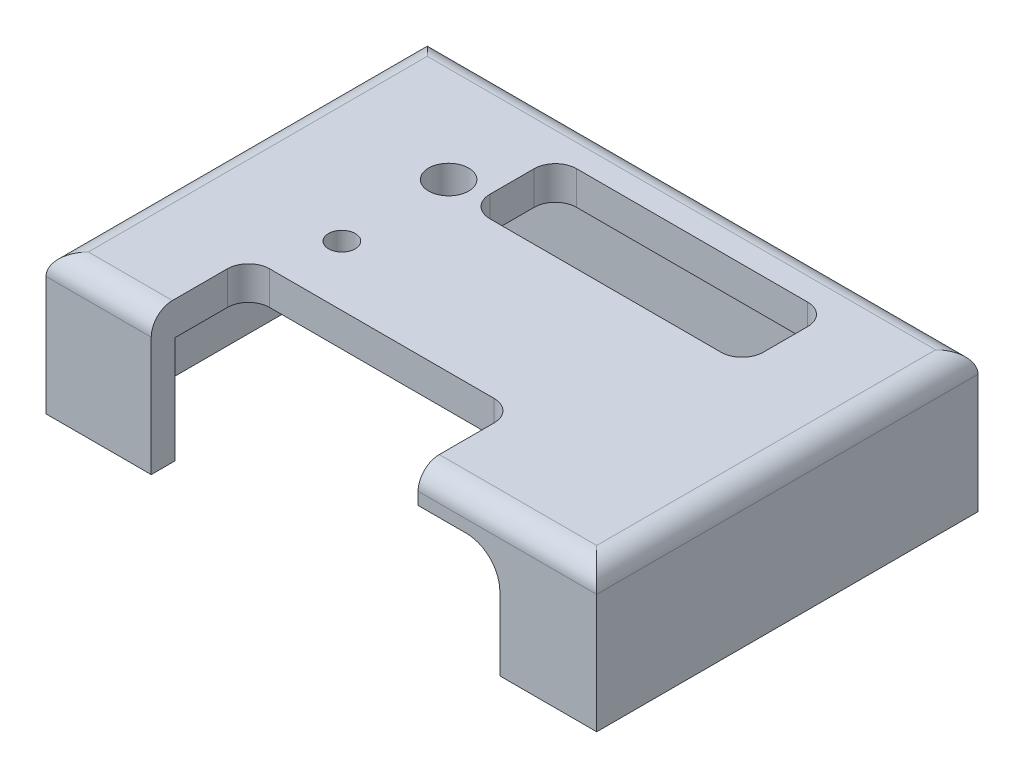
SolidWorks part; units mm, degrees
material "6061-T6 (SS)"
ref_plane "Front Plane" through (0, 0, 0) normal (0, 0, 1) x (1, 0, 0)
ref_plane "Top Plane" through (0, 0, 0) normal (0, 1, 0) x (1, 0, 0)
ref_plane "Right Plane" through (0, 0, 0) normal (1, 0, 0) x (0, 0, -1)
sketch "Sketch1" plane through (0, 0, 0) normal (0, 1, 0) x (1, 0, 0)
  line L1 (41.275, -28.575) -> (-41.275, -28.575)
  line L2 (41.275, -28.575) -> (41.275, 28.575)
  line L3 (41.275, 28.575) -> (-41.275, 28.575)
  line L4 (-41.275, -28.575) -> (-41.275, 28.575)
  line L5 (41.275, -28.575) -> (-41.275, 28.575) construction
  line L6 (41.275, 28.575) -> (-41.275, -28.575) construction
  point P0 (0, 0)
  dimension "D1" = 57.15
  dimension "D2" = 82.55
extrude "Boss-Extrude1" add sketch "Sketch1" along normal blind 21.018
sketch "Sketch2" plane through (0, 0, 0) normal (0, 1, 0) x (1, 0, 0)
  line L1 (30.15, -25) -> (-30.15, -25)
  line L2 (36.5, -18.65) -> (36.5, 18.65)
  line L3 (30.15, 25) -> (-30.15, 25)
  line L4 (-36.5, -18.65) -> (-36.5, 18.65)
  line L5 (36.5, -25) -> (-36.5, 25) construction
  line L6 (36.5, 25) -> (-36.5, -25) construction
  arc A0 (36.5, 18.65) -> (30.15, 25) centre (30.15, 18.65) ccw
  arc A1 (30.15, -25) -> (36.5, -18.65) centre (30.15, -18.65) ccw
  arc A2 (-30.15, -25) -> (-36.5, -18.65) centre (-30.15, -18.65) cw
  arc A3 (-30.15, 25) -> (-36.5, 18.65) centre (-30.15, 18.65) ccw
  point P0 (0, 0)
  dimension "D3" = 6.35
  dimension "D1" = 73
  dimension "D2" = 50
extrude "Cut-Extrude1" cut sketch "Sketch2" along normal blind 16
hole_wizard "#8-32 Tapped Hole1" positions "Sketch3" profile "Sketch4" tap size "#8-32" standard "ANSI Inch"
sketch "Sketch3" plane through (0, 0, 0) normal (0, -1, 0) x (-1, 0, 0)
  point P0 (37.275, -24.575)
  point P3 (37.275, 24.575)
  point P6 (-37.275, -24.575)
  point P9 (-37.275, 24.575)
cosmetic thread "Hole Thread1" parameters "D1"=8.331, "D2"=4.1656
cosmetic thread "Hole Thread2" parameters "D1"=8.331, "D2"=4.1656
cosmetic thread "Hole Thread3" parameters "D1"=8.331, "D2"=4.1656
cosmetic thread "Hole Thread4" parameters "D1"=8.331, "D2"=4.1656
sketch "Sketch4" plane through (-37.275, 0, 24.575) normal (1, 0, 0) x (0, 0, -1)
  line L0 (0, 0) -> (0, 11.7458)
  line L1 (0, 11.7458) -> (1.7272, 10.708)
  line L2 (1.7272, 10.708) -> (1.7272, 0)
  line L5 (1.7272, 0) -> (0, 0)
  line L10 (0, 11.7458) -> (-1.7272, 10.708) construction
  line L11 (0, -6.35) -> (0, 107.95) construction
  dimension "Tap Drill Dia." = 3.4544
  dimension "Tap Drill Depth" = 10.708
  dimension "Drill Angle" = 118
sketch "Sketch5" plane through (0, 21.018, 0) normal (0, 1, 0) x (1, 0, 0)
  line L5 (-15.5, 22) -> (-15.5, 9) construction
  line L6 (-15.5, 9) -> (25.5, 9) construction
  line L7 (25.5, 9) -> (25.5, 22) construction
  line L8 (25.5, 22) -> (-15.5, 22) construction
  line L9 (15, -6) -> (15, -22) construction
  line L10 (15, -22) -> (24.5, -22) construction
  line L11 (24.5, -22) -> (24.5, -6) construction
  line L12 (24.5, -6) -> (15, -6) construction
  line L13 (11, -20.5) -> (11, -15.5) construction
  line L14 (11, -15.5) -> (6, -15.5) construction
  line L15 (6, -15.5) -> (6, -20.5) construction
  line L16 (6, -20.5) -> (11, -20.5) construction
  line L17 (-3, -20.5) -> (-3, -15.5) construction
  line L18 (-3, -15.5) -> (-8, -15.5) construction
  line L19 (-8, -15.5) -> (-8, -20.5) construction
  line L20 (-8, -20.5) -> (-3, -20.5) construction
  line L21 (-17, -20.5) -> (-17, -15.5) construction
  line L22 (-17, -15.5) -> (-22, -15.5) construction
  line L23 (-22, -15.5) -> (-22, -20.5) construction
  line L24 (-22, -20.5) -> (-17, -20.5) construction
  line L25 (-15.5, 22) -> (-15.5, 9)
  line L26 (-15.5, 9) -> (25.5, 9)
  line L27 (25.5, 9) -> (25.5, 22)
  line L28 (25.5, 22) -> (-15.5, 22)
  line L29 (15, -6) -> (15, -22)
  line L30 (15, -22) -> (24.5, -22)
  line L31 (24.5, -22) -> (24.5, -6)
  line L32 (24.5, -6) -> (15, -6)
  line L33 (11, -20.5) -> (11, -15.5)
  line L34 (11, -15.5) -> (6, -15.5)
  line L35 (6, -15.5) -> (6, -20.5)
  line L36 (6, -20.5) -> (11, -20.5)
  line L37 (-3, -20.5) -> (-3, -15.5)
  line L38 (-3, -15.5) -> (-8, -15.5)
  line L39 (-8, -15.5) -> (-8, -20.5)
  line L40 (-8, -20.5) -> (-3, -20.5)
  line L41 (-17, -20.5) -> (-17, -15.5)
  line L42 (-17, -15.5) -> (-22, -15.5)
  line L43 (-22, -15.5) -> (-22, -20.5)
  line L44 (-22, -20.5) -> (-17, -20.5)
  circle A0 centre (-20.5, -5) radius 4.5 construction
  circle A1 centre (-20.5, 11) radius 4.5 construction
  circle A2 centre (-20.5, -5) radius 4.5
  circle A3 centre (-20.5, 11) radius 4.5
fillet "Fillet1" radius 3.175 4 edges at (0, 21.018, -28.575) (41.275, 21.018, 0) (0, 21.018, 28.575) (-41.275, 21.018, 0)
sketch "Sketch6" plane through (0, 21.018, 0) normal (0, 1, 0) x (1, 0, 0)
  line L0 (25.5, 15.5) -> (-15.5, 15.5) construction
  line L1 (-12.325, 9) -> (22.325, 9)
  line L2 (-15.5, 12.175) -> (-15.5, 18.825)
  line L3 (-12.325, 22) -> (22.325, 22)
  line L4 (25.5, 12.175) -> (25.5, 18.825)
  line L5 (-15.5, 9) -> (25.5, 22) construction
  line L6 (-15.5, 22) -> (25.5, 9) construction
  line L7 (25.5, 9) -> (25.5, 22) construction
  line L8 (-15.5, 22) -> (-15.5, 9) construction
  line L9 (-41.275, -28.575) -> (41.275, -28.575) construction
  line L10 (-25.5, -28.575) -> (14.5, -28.575)
  line L11 (-25.5, -28.575) -> (-25.5, -17.175)
  line L12 (-22.325, -14) -> (11.325, -14)
  line L13 (14.5, -28.575) -> (14.5, -17.175)
  line L14 (-5.5, -15.5) -> (-5.5, -14) construction
  line L15 (-3, -15.5) -> (-8, -15.5) construction
  line L16 (-22, -18) -> (11, -18) construction
  line L17 (-22, -15.5) -> (-22, -20.5) construction
  line L18 (11, -20.5) -> (11, -15.5) construction
  arc A0 (22.325, 9) -> (25.5, 12.175) centre (22.325, 12.175) ccw
  arc A1 (22.325, 22) -> (25.5, 18.825) centre (22.325, 18.825) cw
  arc A2 (-12.325, 9) -> (-15.5, 12.175) centre (-12.325, 12.175) cw
  arc A3 (-15.5, 18.825) -> (-12.325, 22) centre (-12.325, 18.825) cw
  circle A4 centre (-20.5, 11) radius 3
  circle A5 centre (-20.5, -5) radius 2
  arc A6 (11.325, -14) -> (14.5, -17.175) centre (11.325, -17.175) cw
  arc A7 (-25.5, -17.175) -> (-22.325, -14) centre (-22.325, -17.175) cw
  point P0 (5, 15.5)
  point P49 (14.5, -14)
  point P52 (-25.5, -14)
  dimension "D3" = 3.175
  dimension "D4" = 6
  dimension "D5" = 4
  dimension "D8" = 3.175
  dimension "D1" = 41
  dimension "D2" = 13
  dimension "D6" = 40
  dimension "D7" = 4
extrude "Cut-Extrude2" cut sketch "Sketch6" against normal through all
sketch "Sketch7" plane through (0, 0, 28.575) normal (0, 0, 1) x (1, 0, 0)
  line L0 (21.75, 16) -> (14.5, 16)
  line L1 (14.5, 0) -> (14.5, 17.843) construction
  line L2 (14.5, 16) -> (14.5, 0)
  line L4 (26.75, 11) -> (26.75, 0)
  line L5 (14.5, 0) -> (41.275, 0) construction
  line L6 (26.75, 0) -> (14.5, 0)
  line L7 (14.5, 16) -> (30.15, 16) construction
  arc A0 (26.75, 11) -> (21.75, 16) centre (21.75, 11) ccw
  dimension "D2" = 10
  dimension "D1" = 21.75
  dimension "D3" = 11
extrude "Cut-Extrude3" cut sketch "Sketch7" against normal up to next
